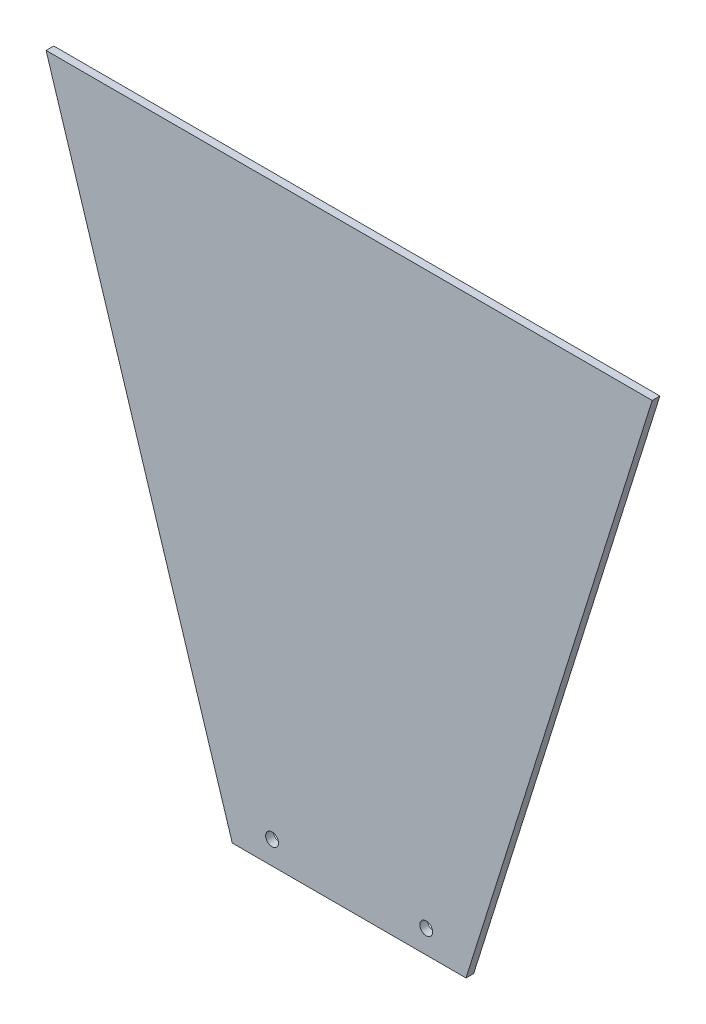
SolidWorks part; units mm, degrees
ref_plane "Alzado" through (0, 0, 0) normal (0, 0, 1) x (1, 0, 0)
ref_plane "Planta" through (0, 0, 0) normal (0, 1, 0) x (1, 0, 0)
ref_plane "Vista lateral" through (0, 0, 0) normal (1, 0, 0) x (0, 0, -1)
sketch "Croquis1" plane through (0, 0, 0) normal (0, 0, 1) x (1, 0, 0)
  line L0 (-45.5, 0) -> (-118, 231)
  line L1 (-118, 231) -> (118, 231)
  line L2 (118, 231) -> (45.5, 0)
  line L3 (-45.5, 0) -> (45.5, 0)
  line L4 (-77.5065, 9) -> (71.6496, 9) construction
  circle A0 centre (-30, 9) radius 2.5
  circle A1 centre (30, 9) radius 2.5
  point P12 (0, 0)
  dimension "D5" = 5
  dimension "D1" = 236
  dimension "D2" = 231
  dimension "D3" = 91
  dimension "D4" = 118
  dimension "D6" = 9
  dimension "D7" = 30
  dimension "D8" = 30
extrude "Saliente-Extruir1" add sketch "Croquis1" along normal blind 3
